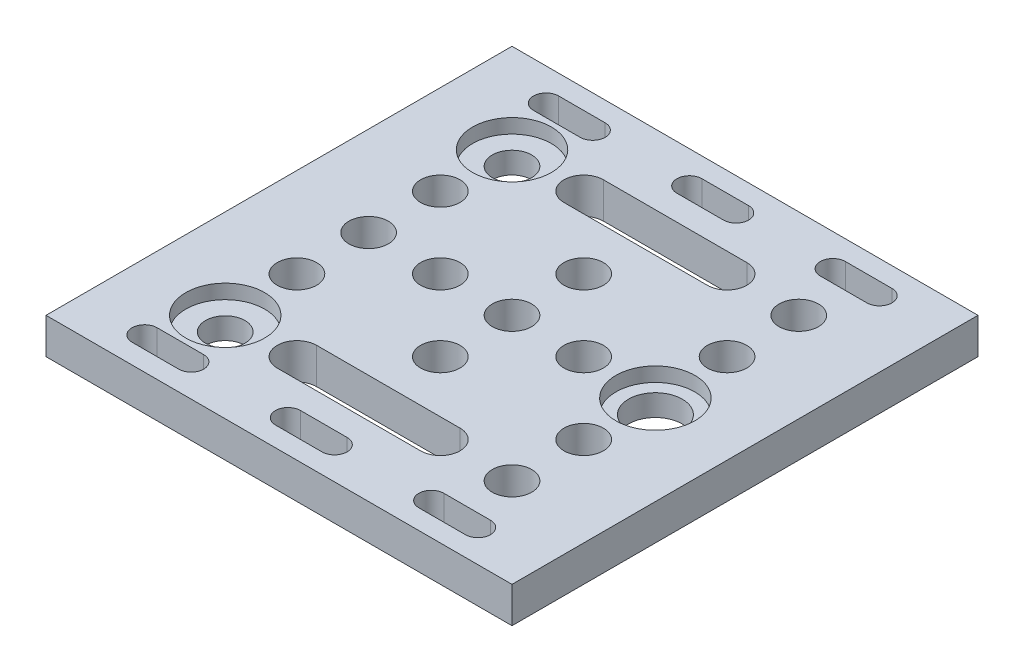
SolidWorks part; units mm, degrees
ref_plane "Front Plane" through (0, 0, 0) normal (0, 0, 1) x (1, 0, 0)
ref_plane "Top Plane" through (0, 0, 0) normal (0, 1, 0) x (1, 0, 0)
ref_plane "Right Plane" through (0, 0, 0) normal (1, 0, 0) x (0, 0, -1)
sketch "Sketch1" plane through (0, 0, 0) normal (0, 1, 0) x (1, 0, 0)
  line L0 (0, 32.5) -> (12.5, 32.5) construction
  line L1 (0, 0) -> (65, 0)
  line L2 (0, 0) -> (0, 65)
  line L3 (0, 65) -> (65, 65)
  line L4 (65, 0) -> (65, 65)
  line L5 (32.5, 65) -> (32.5, 42.5) construction
  line L6 (32.5, 65) -> (32.5, 52.5) construction
  line L7 (32.5, 65) -> (32.5, 60.5) construction
  line L8 (0, 32.5) -> (22.5, 32.5) construction
  line L9 (0, 32.5) -> (65, 32.5) construction
  line L10 (12.5, 32.5) -> (12.5, 42.5) construction
  line L11 (12.5, 42.5) -> (32.5, 42.5) construction
  line L12 (22.5, 52.5) -> (42.5, 52.5) construction
  line L13 (22.5, 55.25) -> (42.5, 55.25)
  line L14 (22.5, 49.75) -> (42.5, 49.75)
  line L15 (29.25, 60.5) -> (35.75, 60.5) construction
  line L16 (29.25, 62.25) -> (35.75, 62.25)
  line L17 (29.25, 58.75) -> (35.75, 58.75)
  line L18 (12.5, 42.5) -> (12.5, 60.5) construction
  line L19 (12.5, 60.5) -> (32.5, 60.5) construction
  line L20 (9.25, 60.5) -> (15.75, 60.5) construction
  line L21 (9.25, 62.25) -> (15.75, 62.25)
  line L22 (9.25, 58.75) -> (15.75, 58.75)
  line L23 (32.5, 52.5) -> (12.5, 52.5) construction
  line L24 (32.5, 65) -> (32.5, 0) construction
  line L25 (55.75, 60.5) -> (49.25, 60.5) construction
  line L26 (55.75, 62.25) -> (49.25, 62.25)
  line L27 (55.75, 58.75) -> (49.25, 58.75)
  line L28 (22.5, 12.5) -> (42.5, 12.5) construction
  line L29 (22.5, 9.75) -> (42.5, 9.75)
  line L30 (22.5, 15.25) -> (42.5, 15.25)
  line L31 (55.75, 4.5) -> (49.25, 4.5) construction
  line L32 (55.75, 2.75) -> (49.25, 2.75)
  line L33 (55.75, 6.25) -> (49.25, 6.25)
  line L34 (9.25, 4.5) -> (15.75, 4.5) construction
  line L35 (9.25, 2.75) -> (15.75, 2.75)
  line L36 (9.25, 6.25) -> (15.75, 6.25)
  line L37 (29.25, 4.5) -> (35.75, 4.5) construction
  line L38 (29.25, 2.75) -> (35.75, 2.75)
  line L39 (29.25, 6.25) -> (35.75, 6.25)
  line L40 (32.5, 52.5) -> (52.5, 52.5) construction
  circle A0 centre (32.5, 32.5) radius 2.75
  circle A1 centre (22.5, 32.5) radius 2.75
  circle A2 centre (12.5, 32.5) radius 2.75
  circle A3 centre (32.5, 42.5) radius 2.75
  circle A4 centre (12.5, 42.5) radius 2.75
  arc A5 (22.5, 55.25) -> (22.5, 49.75) centre (22.5, 52.5) ccw
  arc A6 (42.5, 49.75) -> (42.5, 55.25) centre (42.5, 52.5) ccw
  arc A7 (29.25, 62.25) -> (29.25, 58.75) centre (29.25, 60.5) ccw
  arc A8 (35.75, 58.75) -> (35.75, 62.25) centre (35.75, 60.5) ccw
  arc A9 (9.25, 62.25) -> (9.25, 58.75) centre (9.25, 60.5) ccw
  arc A10 (15.75, 58.75) -> (15.75, 62.25) centre (15.75, 60.5) ccw
  circle A11 centre (12.5, 52.5) radius 2.75
  circle A12 centre (42.5, 32.5) radius 2.75
  circle A13 centre (52.5, 32.5) radius 3.75
  circle A14 centre (52.5, 42.5) radius 2.75
  arc A16 (55.75, 62.25) -> (55.75, 58.75) centre (55.75, 60.5) cw
  arc A17 (49.25, 58.75) -> (49.25, 62.25) centre (49.25, 60.5) cw
  circle A18 centre (52.5, 22.5) radius 2.75
  circle A19 centre (32.5, 22.5) radius 2.75
  circle A20 centre (12.5, 22.5) radius 2.75
  arc A22 (22.5, 9.75) -> (22.5, 15.25) centre (22.5, 12.5) cw
  arc A23 (42.5, 15.25) -> (42.5, 9.75) centre (42.5, 12.5) cw
  arc A24 (55.75, 2.75) -> (55.75, 6.25) centre (55.75, 4.5) ccw
  arc A25 (49.25, 6.25) -> (49.25, 2.75) centre (49.25, 4.5) ccw
  arc A26 (9.25, 2.75) -> (9.25, 6.25) centre (9.25, 4.5) cw
  arc A27 (15.75, 6.25) -> (15.75, 2.75) centre (15.75, 4.5) cw
  arc A28 (29.25, 2.75) -> (29.25, 6.25) centre (29.25, 4.5) cw
  arc A29 (35.75, 6.25) -> (35.75, 2.75) centre (35.75, 4.5) cw
  circle A30 centre (12.5, 12.5) radius 2.75
  circle A31 centre (52.5, 52.5) radius 2.75
  circle A32 centre (52.5, 12.5) radius 2.75
  point P22 (32.5, 52.5)
  point P27 (19.75, 52.5)
  point P28 (45.25, 52.5)
  point P31 (32.5, 60.5)
  point P36 (27.5, 60.5)
  point P37 (37.5, 60.5)
  point P41 (12.5, 60.5)
  point P46 (7.5, 60.5)
  point P47 (17.5, 60.5)
  point P61 (52.5, 60.5)
  point P76 (32.5, 12.5)
  point P83 (52.5, 4.5)
  point P90 (12.5, 4.5)
  point P97 (32.5, 4.5)
  dimension "D8" = 5.5
  dimension "D9" = 5.5
  dimension "D10" = 5.5
  dimension "D11" = 5.5
  dimension "D12" = 5.5
  dimension "D19" = 7.5
  dimension "D1" = 65
  dimension "D2" = 65
  dimension "D3" = 12.5
  dimension "D4" = 22.5
  dimension "D5" = 12.5
  dimension "D6" = 4.5
  dimension "D7" = 22.5
  dimension "D13" = 25.5
  dimension "D14" = 5.5
  dimension "D15" = 3.5
  dimension "D16" = 10
  dimension "D17" = 10
  dimension "D18" = 3.5
  dimension "D21" = 20
extrude "Boss-Extrude1" add sketch "Sketch1" along normal blind 5
sketch "Sketch2" plane through (0, 5, 0) normal (0, 1, 0) x (1, 0, 0)
  circle A0 centre (12.5, 52.5) radius 5.5
  circle A1 centre (52.5, 32.5) radius 5.5
  circle A2 centre (12.5, 12.5) radius 5.5
  dimension "D1" = 11
  dimension "D2" = 11
  dimension "D3" = 11
extrude "Cut-Extrude1" cut sketch "Sketch2" against normal blind 2
